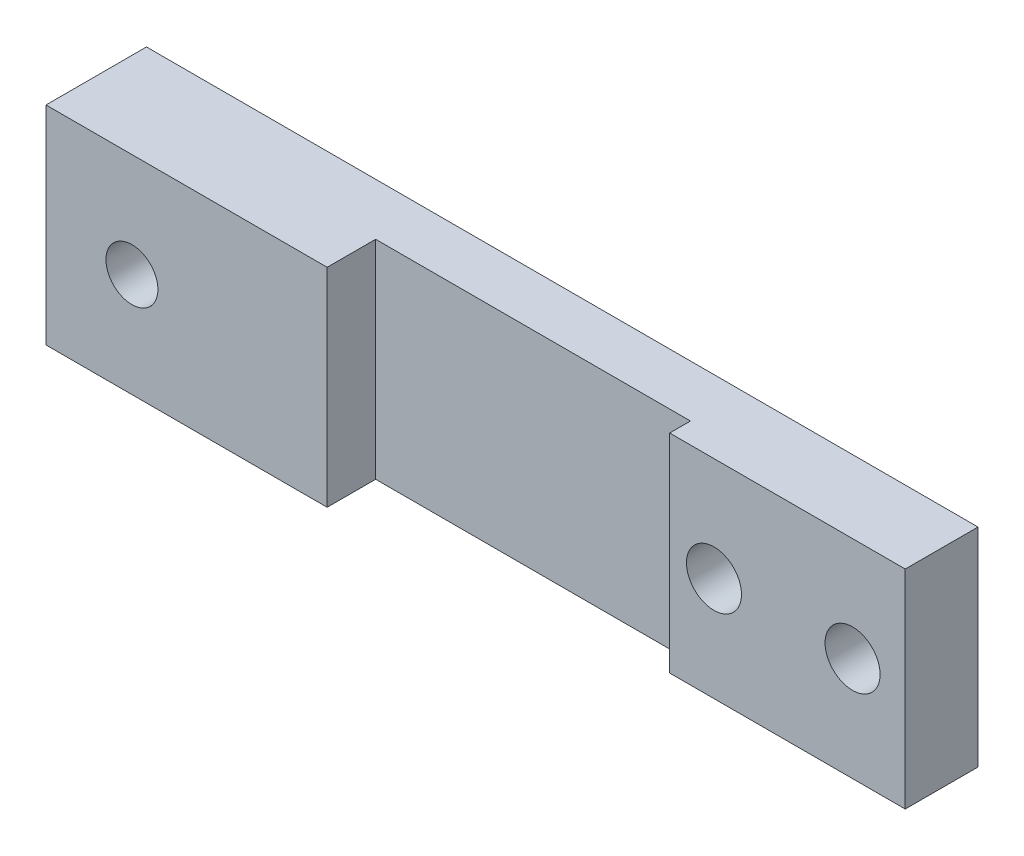
SolidWorks part; units mm, degrees
material "1060 Alloy"
ref_plane "Front Plane" through (0, 0, 0) normal (0, 0, 1) x (1, 0, 0)
ref_plane "Top Plane" through (0, 0, 0) normal (0, 1, 0) x (1, 0, 0)
ref_plane "Right Plane" through (0, 0, 0) normal (1, 0, 0) x (0, 0, -1)
sketch "Sketch1" plane through (0, 0, 0) normal (0, 0, 1) x (1, 0, 0)
  line L1 (76.2, 19.05) -> (-76.2, 19.05)
  line L2 (76.2, 19.05) -> (76.2, -19.05)
  line L3 (76.2, -19.05) -> (-76.2, -19.05)
  line L4 (-76.2, 19.05) -> (-76.2, -19.05)
  line L5 (76.2, 19.05) -> (-76.2, -19.05) construction
  line L6 (76.2, -19.05) -> (-76.2, 19.05) construction
  point P0 (0, 0)
  dimension "D1" = 152.4
  dimension "D2" = 38.1
extrude "Boss-Extrude1" add sketch "Sketch1" along normal blind 9.525
sketch "Sketch5" plane through (0, 0, 9.525) normal (0, 0, 1) x (1, 0, 0)
  line L0 (33.02, 19.05) -> (33.02, -19.05)
  line L1 (76.2, 19.05) -> (-76.2, 19.05) construction
  line L2 (-76.2, -19.05) -> (76.2, -19.05) construction
  line L3 (33.02, -19.05) -> (76.2, -19.05)
  line L4 (76.2, -19.05) -> (76.2, 19.05)
  line L5 (76.2, 19.05) -> (33.02, 19.05)
  dimension "D1" = 43.18
extrude "Boss-Extrude3" add sketch "Sketch5" along normal blind 3.81
hole_wizard "3/8 Clearance Hole1" positions "Sketch2" profile "Sketch3" hole size "3/8" standard "ANSI Inch"
sketch "Sketch2" plane through (0, 0, 9.525) normal (0, 0, 1) x (1, 0, 0)
  line L0 (76.2, -19.05) -> (76.2, 19.05) construction
  point P2 (41.148, 0)
  point P4 (66.548, 0)
  dimension "D1" = 25.4
  dimension "D2" = 9.652
sketch "Sketch3" plane through (41.148, 0, 9.525) normal (1, 0, 0) x (0, 1, 0)
  line L0 (0, 0) -> (0, 3.81)
  line L1 (0, 3.81) -> (5.0419, 3.81)
  line L2 (5.0419, 3.81) -> (5.0419, 0)
  line L5 (5.0419, 0) -> (0, 0)
  line L11 (0, -6.35) -> (0, 107.95) construction
  dimension "Thru Hole Dia." = 10.0838
  dimension "Thru Hole Depth" = 3.81
sketch "Sketch4" plane through (0, 0, 9.525) normal (0, 0, 1) x (1, 0, 0)
  line L0 (-76.2, 19.05) -> (-76.2, -19.05)
  line L1 (-76.2, -19.05) -> (-24.6715, -19.05)
  line L2 (-76.2, -19.05) -> (33.02, -19.05) construction
  line L3 (-24.6715, -19.05) -> (-24.6715, 19.05)
  line L4 (33.02, 19.05) -> (-76.2, 19.05) construction
  line L5 (-24.6715, 19.05) -> (-76.2, 19.05)
extrude "Boss-Extrude2" add sketch "Sketch4" along normal blind 8.89
hole_wizard "3/8 Clearance Hole3" positions "Sketch8" profile "Sketch9" hole size "3/8" standard "ANSI Inch" end condition through all
sketch "Sketch8" plane through (0, 0, 0) normal (0, 0, -1) x (-1, 0, 0)
  point P0 (-66.548, 0)
  point P3 (-41.148, 0)
sketch "Sketch9" plane through (66.548, 0, 0) normal (1, 0, 0) x (0, 1, 0)
  line L0 (0, 0) -> (0, 18.415)
  line L1 (0, 18.415) -> (5.0419, 18.415)
  line L2 (5.0419, 18.415) -> (5.0419, 0)
  line L5 (5.0419, 0) -> (0, 0)
  line L11 (0, -6.35) -> (0, 107.95) construction
  dimension "Thru Hole Dia." = 10.0838
  dimension "Thru Hole Depth" = 18.415
sketch "Sketch10" plane through (0, 0, 18.415) normal (0, 0, 1) x (1, 0, 0)
  line L1 (-76.2, 19.05) -> (-76.2, -19.05) construction
  circle A0 centre (-60.452, 0) radius 4.7625
  circle A1 centre (41.148, 0) radius 5.0419 construction
  point P9 (-76.2, 0)
  dimension "D1" = 101.6
  dimension "D2" = 9.525
extrude "Cut-Extrude1" cut sketch "Sketch10" against normal through all
